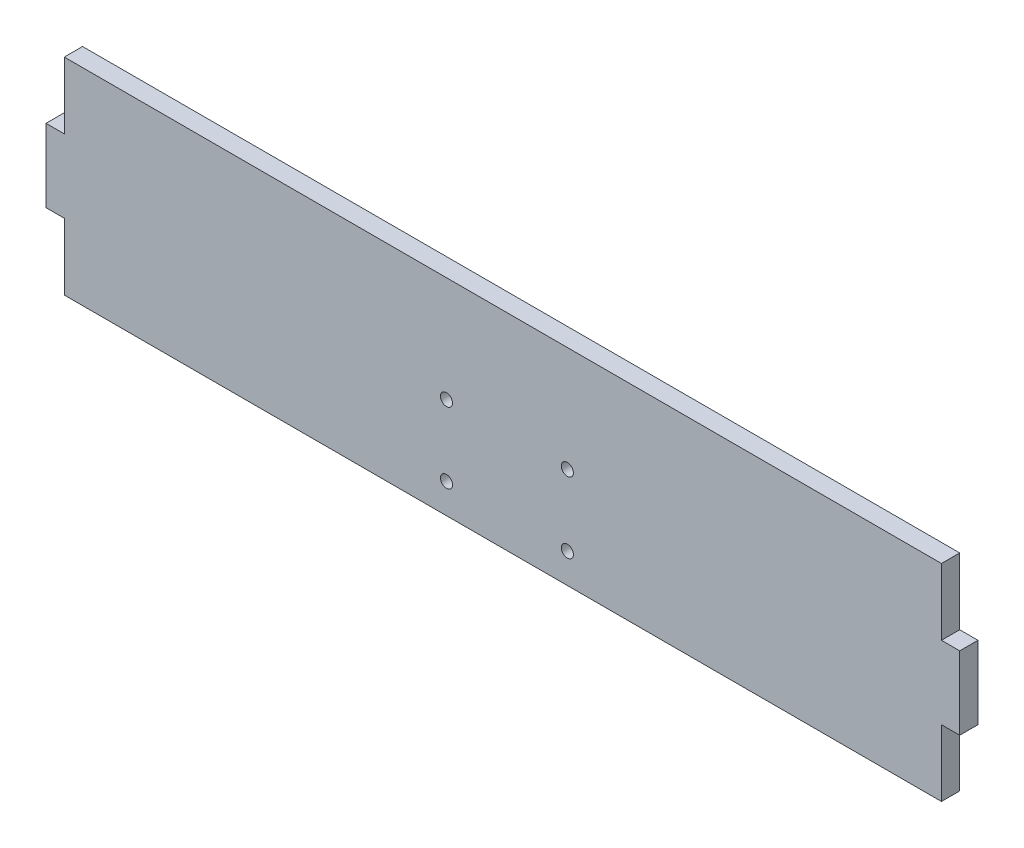
SolidWorks part; units mm, degrees
ref_plane "Front" through (0, 0, 0) normal (0, 0, 1) x (1, 0, 0)
ref_plane "Top" through (0, 0, 0) normal (0, 1, 0) x (1, 0, 0)
ref_plane "Right" through (0, 0, 0) normal (1, 0, 0) x (0, 0, -1)
sketch "Sketch1" plane through (0, 0, 0) normal (0, 0, 1) x (1, 0, 0)
  line L1 (0, 0) -> (158.75, 0)
  line L2 (0, 0) -> (0, 35.814)
  line L3 (0, 35.814) -> (158.75, 35.814)
  line L4 (158.75, 0) -> (158.75, 35.814)
  dimension "D1" = 158.75
  dimension "D2" = 35.814
extrude "Boss-Extrude1" add sketch "Sketch1" along normal blind 3.175
sketch "Sketch2" plane through (0, 0, 3.175) normal (0, 0, 1) x (1, 0, 0)
  line L0 (0, 17.907) -> (158.75, 17.907) construction
  line L1 (0, 35.814) -> (0, 0) construction
  line L2 (158.75, 0) -> (158.75, 35.814) construction
  line L3 (79.375, 35.814) -> (79.375, 0) construction
  line L4 (158.75, 35.814) -> (0, 35.814) construction
  line L5 (0, 0) -> (158.75, 0) construction
  line L6 (158.75, 11.557) -> (155.575, 11.557)
  line L7 (0, 0) -> (3.175, 0)
  line L8 (0, 0) -> (0, 11.557)
  line L9 (0, 11.557) -> (3.175, 11.557)
  line L10 (3.175, 0) -> (3.175, 11.557)
  line L11 (0, 35.814) -> (3.175, 35.814)
  line L12 (0, 35.814) -> (0, 24.257)
  line L13 (0, 24.257) -> (3.175, 24.257)
  line L14 (3.175, 35.814) -> (3.175, 24.257)
  line L15 (155.575, 0) -> (155.575, 11.557)
  line L16 (158.75, 0) -> (155.575, 0)
  line L17 (158.75, 0) -> (158.75, 11.557)
  line L18 (158.75, 24.257) -> (155.575, 24.257)
  line L19 (155.575, 35.814) -> (155.575, 24.257)
  line L20 (158.75, 35.814) -> (155.575, 35.814)
  line L21 (158.75, 35.814) -> (158.75, 24.257)
  dimension "D1" = 12.7
  dimension "D2" = 3.175
extrude "Cut-Extrude1" cut sketch "Sketch2" against normal through all
sketch "Sketch3" plane through (0, 0, 0) normal (0, 0, -1) x (-1, 0, 0)
  line L1 (-79.375, 35.814) -> (-79.375, 0) construction
  line L2 (-155.575, 35.814) -> (-3.175, 35.814) construction
  line L3 (-3.175, 0) -> (-155.575, 0) construction
  line L4 (0, 17.907) -> (-158.75, 17.907) construction
  line L5 (0, 24.257) -> (0, 11.557) construction
  line L6 (-158.75, 11.557) -> (-158.75, 24.257) construction
  circle A0 centre (-90.5789, 17.4718) radius 1.05
  circle A1 centre (-69.5789, 5.1718) radius 1.05
  circle A2 centre (-90.5789, 5.1718) radius 1.05
  circle A3 centre (-69.5789, 17.4718) radius 1.05
extrude "Cut-Extrude2" cut sketch "Sketch3" against normal through all
